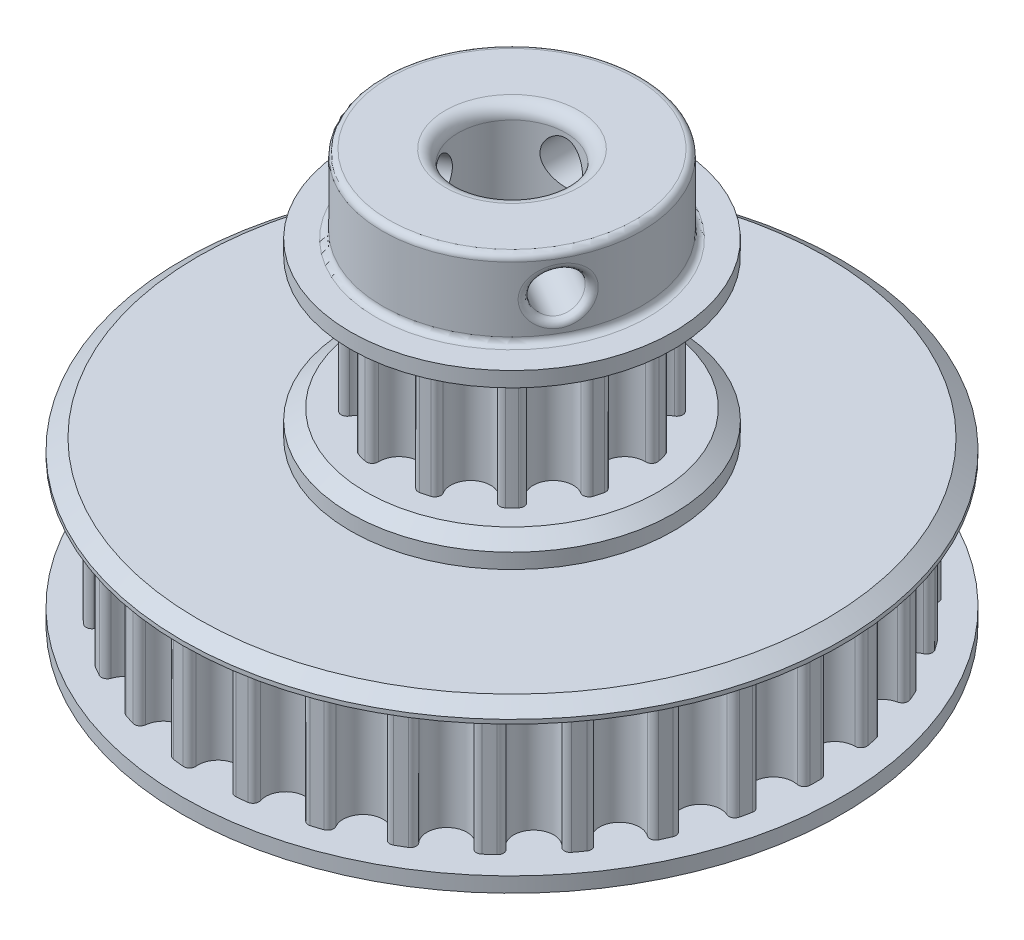
SolidWorks part; units mm, degrees
ref_plane "Plan de face" through (0, 0, 0) normal (0, 0, 1) x (1, 0, 0)
ref_plane "Plan de dessus" through (0, 0, 0) normal (0, 1, 0) x (1, 0, 0)
ref_plane "Plan de droite" through (0, 0, 0) normal (1, 0, 0) x (0, 0, -1)
sketch "Esquisse1" plane through (0, 0, 0) normal (0, 1, 0) x (1, 0, 0)
  line L0 (0, 0) -> (-2.449, 9.1398)
  line L2 (2.449, 9.1398) -> (0, 0)
  line L3 (0, 9.4622) -> (0, 0) construction
  line L4 (-2.449, 9.1398) -> (2.449, 9.1398) construction
  circle A1 centre (0, 0) radius 9.4622 construction
  arc A2 (-1.5419, 8.7624) -> (1.5419, 8.7624) centre (0, 8.7052) ccw
  arc A3 (-2.449, 9.1398) -> (-2.1013, 9.2259) centre (0, 0) cw
  arc A4 (-2.1013, 9.2259) -> (-1.5419, 8.7624) centre (-1.9996, 8.7794) cw
  arc A5 (2.449, 9.1398) -> (2.1013, 9.2259) centre (0, 0) ccw
  arc A6 (2.1013, 9.2259) -> (1.5419, 8.7624) centre (1.9996, 8.7794) ccw
  arc A7 (-1.5419, 8.7624) -> (-1.3979, 9.3584) centre (0, 8.7052) cw construction
  arc A8 (1.5419, 8.7624) -> (1.3979, 9.3584) centre (0, 8.7052) ccw construction
  point P6 (0, 7.1622)
  dimension "D2" = 1.543
  dimension "D3" = 0.458
  dimension "D1" = 4.898
  dimension "D4" = 2.3
  dimension "D5" = 30
extrude "Boss.-Extru.1" add sketch "Esquisse1" along normal blind 9.3
pattern_circular "Répétition circulaire1" count 12 over 360 about axis through (0, 0, 0) along (0, 1, 0) of "Boss.-Extru.1"
ref_plane "Plan1" through (0, 4.65, 0) normal (0, -1, 0) x (-1, 0, 0)
sketch "Esquisse2" plane through (0, 9.3, 0) normal (0, 1, 0) x (1, 0, 0)
  circle A0 centre (0, 0) radius 12.4622
  arc A1 (-9.2259, -2.1013) -> (-9.0406, -2.7932) centre (0, 0) ccw construction
  dimension "D1" = 3
extrude "Boss.-Extru.2" add sketch "Esquisse2" along normal blind 2
mirror "Symétrie1" about plane through (0, 4.65, 0) normal (0, -1, 0) of "Boss.-Extru.2"
sketch "Esquisse4" plane through (0, 11.3, 0) normal (0, 1, 0) x (1, 0, 0)
  circle A0 centre (0, 0) radius 10
  dimension "D1" = 20
extrude "Boss.-Extru.3" add sketch "Esquisse4" along normal blind 6
sketch "Esquisse5" plane through (0, 0, 0) normal (0, 0, 1) x (1, 0, 0)
  line L0 (0, 0) -> (0, 14.3) construction
  line L1 (10, 17.3) -> (-10, 17.3) construction
  circle A0 centre (0, 14.3) radius 1.65
  dimension "D2" = 3.3
  dimension "D1" = 3
extrude "Enlèv. mat.-Extru.2" cut sketch "Esquisse5" against normal through all
pattern_circular "Répétition circulaire2" count 3 over 360 about axis through (0, 17.3, 0) along (0, -1, 0) of "Enlèv. mat.-Extru.2"
sketch "Esquisse10" plane through (0, -2, 0) normal (0, -1, 0) x (1, 0, 0)
  circle A0 centre (0, 0) radius 12.4622
  circle A1 centre (0, 0) radius 12.4622 construction
extrude "Boss.-Extru.6" add sketch "Esquisse10" along normal blind 2
sketch "Esquisse7" plane through (0, -4, 0) normal (0, 1, 0) x (1, 0, 0)
  line L0 (0, 0) -> (-2.449, 23.3007)
  line L2 (2.449, 23.3007) -> (0, 0)
  line L3 (0, 23.429) -> (0, 0) construction
  line L4 (-2.449, 23.3007) -> (2.449, 23.3007) construction
  circle A1 centre (0, 0) radius 23.429 construction
  arc A2 (-1.5343, 22.836) -> (1.5343, 22.836) centre (0, 22.672) ccw
  arc A3 (-2.449, 23.3007) -> (-2.0293, 23.341) centre (0, 0) cw
  arc A4 (-2.0293, 23.341) -> (-1.5343, 22.836) centre (-1.9897, 22.8847) cw
  arc A5 (2.449, 23.3007) -> (2.0293, 23.341) centre (0, 0) ccw
  arc A6 (2.0293, 23.341) -> (1.5343, 22.836) centre (1.9897, 22.8847) ccw
  arc A7 (-1.5343, 22.836) -> (-1.3662, 23.3892) centre (0, 22.672) cw construction
  arc A8 (1.5343, 22.836) -> (1.3662, 23.3892) centre (0, 22.672) ccw construction
  point P2 (0, 21.129)
  dimension "D1" = 1.543
  dimension "D2" = 0.458
  dimension "D3" = 2.3
  dimension "D4" = 4.898
  dimension "D5" = 12
extrude "Boss.-Extru.4" add sketch "Esquisse7" against normal blind 9.3
pattern_circular "Répétition circulaire3" count 30 over 360 about axis through (0, 0, 0) along (0, 1, 0) of "Boss.-Extru.4"
ref_plane "Plan2" through (0, -8.65, 0) normal (0, 1, 0) x (1, 0, 0)
sketch "Esquisse9" plane through (0, -4, 0) normal (0, 1, 0) x (1, 0, 0)
  circle A0 centre (0, 0) radius 25.429
  arc A1 (-11.3475, 20.4976) -> (-12.0777, 20.0761) centre (0, 0) ccw construction
  dimension "D1" = 2
extrude "Boss.-Extru.5" add sketch "Esquisse9" along normal blind 2
mirror "Symétrie2" about plane through (0, -8.65, 0) normal (0, 1, 0) of "Boss.-Extru.5"
chamfer "Chanfrein1" distance 1.2 angle 35 5 edges at (0, 9.3, 12.4622) (0, 0, 12.4622) (0, -2, 25.429) (0, -4, 25.429) (0, -15.3, 25.429)
sketch "Esquisse3" plane through (0, 17.3, 0) normal (0, 1, 0) x (1, 0, 0)
  circle A0 centre (0, 0) radius 4.15
  dimension "D1" = 8.3
extrude "Enlèv. mat.-Extru.3" cut sketch "Esquisse3" against normal through all contours A0
fillet "Congé2" radius 0.5 5 edges at (0, 11.3, 10) (0, 17.3, 10) (0.3544, 12.6885, -9.9937) (-7.7413, 13.9455, 6.3302) (9.3528, 13.9455, 3.5391)
fillet "Congé3" radius 1 2 edges at (0, 17.3, 4.15) (0, -15.3, 4.15)
equation "\"nb_tooth1\"= 12"
equation "\"D5@Esquisse1\"=360/\"nb_tooth1\""
equation "\"D1@Répétition circulaire1\"=\"nb_tooth1\""
equation "\"nb_tooth2\"= 30"
equation "\"D5@Esquisse7\"=360/\"nb_tooth2\""
equation "\"D1@Répétition circulaire3\"=\"nb_tooth2\""
